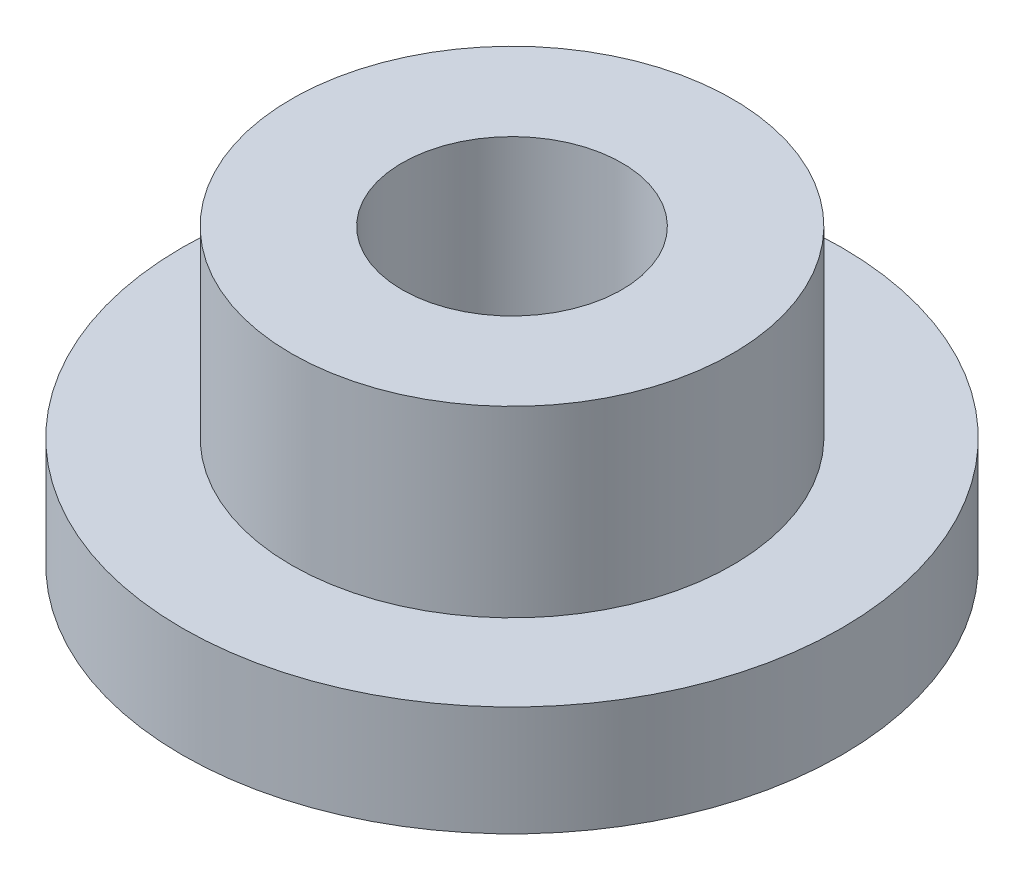
SolidWorks part; units mm, degrees
ref_plane "Front" through (0, 0, 0) normal (0, 0, 1) x (1, 0, 0)
ref_plane "Top" through (0, 0, 0) normal (0, 1, 0) x (1, 0, 0)
ref_plane "Right" through (0, 0, 0) normal (1, 0, 0) x (0, 0, -1)
sketch "Sketch1" plane through (0, 0, 0) normal (0, 1, 0) x (1, 0, 0)
  circle A0 centre (0, 0) radius 1.5
  circle A1 centre (0, 0) radius 3.01
  circle A2 centre (0, 0) radius 4.5
  dimension "ID" = 3
  dimension "OD" = 6.02
  dimension "FlangeOD" = 9
sketch "Sketch2" plane through (0, 0, 0) normal (0, 1, 0) x (1, 0, 0)
  circle A0 centre (0, 0) radius 1.5 construction
  circle A1 centre (0, 0) radius 3.01 construction
  circle A2 centre (0, 0) radius 1.5
  circle A3 centre (0, 0) radius 3.01
extrude "Boss-Extrude1" add sketch "Sketch2" along normal blind 4
sketch "Sketch3" plane through (0, 0, 0) normal (0, 1, 0) x (1, 0, 0)
  circle A0 centre (0, 0) radius 4.5 construction
  circle A1 centre (0, 0) radius 3.01 construction
  circle A2 centre (0, 0) radius 4.5
  circle A3 centre (0, 0) radius 3.01
extrude "Boss-Extrude2" add sketch "Sketch3" along normal blind 1.5
